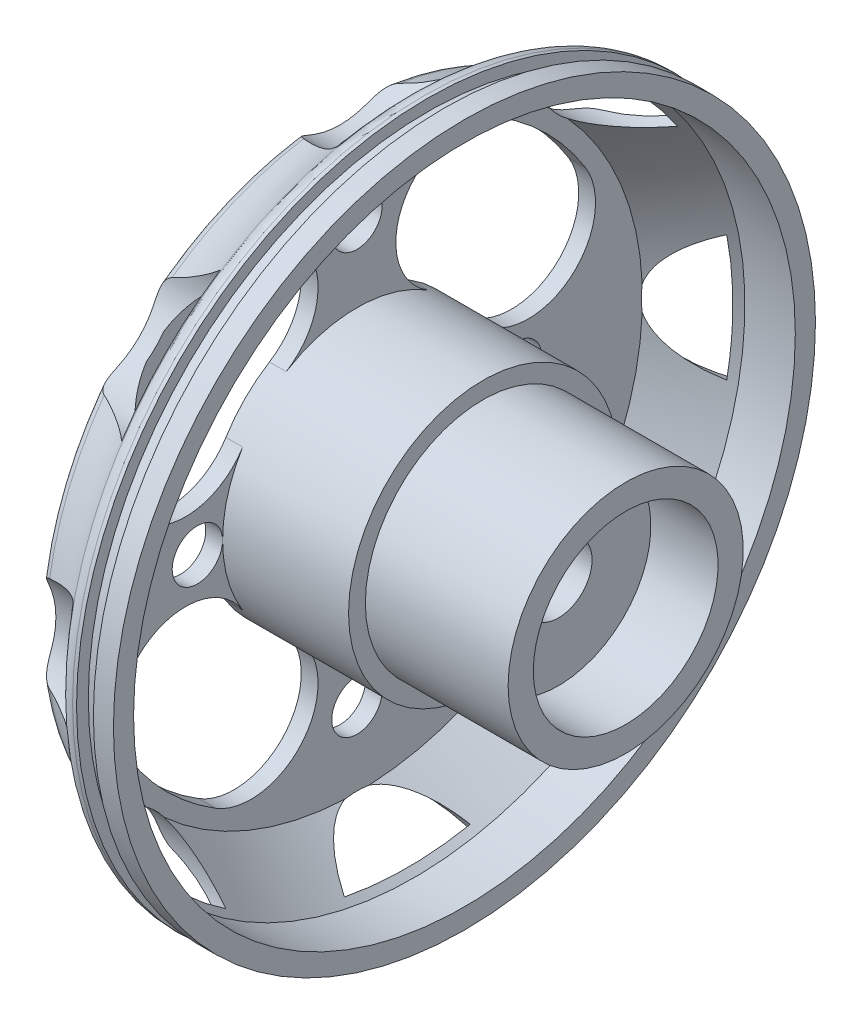
SolidWorks part; units mm, degrees
ref_plane "Front Plane" through (0, 0, 0) normal (0, 0, 1) x (1, 0, 0)
ref_plane "Top Plane" through (0, 0, 0) normal (0, 1, 0) x (1, 0, 0)
ref_plane "Right Plane" through (0, 0, 0) normal (1, 0, 0) x (0, 0, -1)
sketch "Sketch1" plane through (0, 0, 0) normal (0, 0, 1) x (1, 0, 0)
  line L0 (0, 143.0774) -> (0, 0) construction
  line L1 (0, 0) -> (157.1506, 0) construction
  line L2 (170, 55) -> (130, 55)
  line L3 (130, 55) -> (130, 20)
  line L4 (130, 20) -> (40, 20)
  line L5 (40, 20) -> (40, 55)
  line L6 (40, 55) -> (0, 55)
  line L7 (0, 55) -> (0, 87.7801)
  line L10 (74, 197) -> (44, 197)
  line L11 (44, 197) -> (10, 170)
  line L12 (10, 170) -> (10, 80)
  line L13 (10, 80) -> (85, 80)
  line L14 (85, 80) -> (85, 70)
  line L15 (85, 70) -> (170, 70)
  line L16 (170, 70) -> (170, 55)
  line L17 (74, 197) -> (74, 209)
  line L19 (0, 87.7801) -> (0, 180)
  line L20 (52.0391, 209) -> (45, 209)
  line L21 (52.0391, 209) -> (52.0391, 201.9891)
  line L22 (52.0391, 201.9891) -> (62.0706, 201.9891)
  line L23 (62.0706, 201.9891) -> (62.0706, 209)
  line L24 (62.0706, 209) -> (74, 209)
  arc A3 (0, 180) -> (45, 209) centre (-19.7325, 260.0332) ccw
  dimension "D12" = 45
  dimension "D1" = 20
  dimension "D2" = 40
  dimension "D3" = 55
  dimension "D4" = 10
  dimension "D5" = 70
  dimension "D6" = 80
  dimension "D7" = 40
  dimension "D8" = 45
  dimension "D9" = 170
  dimension "D10" = 55
  dimension "D11" = 90
  dimension "D13" = 12
  dimension "D14" = 30
  dimension "D15" = 29
  dimension "D16" = 209
  dimension "D17" = 180
  dimension "D18" = 15
revolve "Revolve1" add sketch "Sketch1" angle 360 about L1
fillet "Fillet1" radius 10 1 edges at (0, 0, 180)
fillet "Fillet2" radius 10 1 edges at (45, 0, 209)
sketch "Sketch5" plane through (0, 0, 0) normal (-1, 0, 0) x (0, 0, 1)
  line L0 (0, 205.6032) -> (0, 0) construction
  line L1 (0, 0) -> (205.6032, 0) construction
  line L2 (0, 0) -> (145.3834, 145.3834) construction
  circle A0 centre (0, 0) radius 205.6032 construction
  arc A1 (102.0401, 63.1492) -> (63.1492, 102.0401) centre (0, 0) ccw construction
  arc A2 (136.0534, 84.1989) -> (84.1989, 136.0534) centre (0, 0) ccw
  arc A3 (68.0267, 42.0995) -> (42.0995, 68.0267) centre (0, 0) ccw
  arc A4 (68.0267, 42.0995) -> (136.0534, 84.1989) centre (102.0401, 63.1492) ccw
  arc A5 (84.1989, 136.0534) -> (42.0995, 68.0267) centre (63.1492, 102.0401) ccw
  arc A6 (42.0995, -68.0267) -> (68.0267, -42.0995) centre (0, 0) ccw
  arc A7 (42.0995, -68.0267) -> (84.1989, -136.0534) centre (63.1492, -102.0401) ccw
  arc A8 (136.0534, -84.1989) -> (68.0267, -42.0995) centre (102.0401, -63.1492) ccw
  arc A9 (84.1989, -136.0534) -> (136.0534, -84.1989) centre (0, 0) ccw
  arc A10 (63.1492, -102.0401) -> (102.0401, -63.1492) centre (0, 0) ccw construction
  arc A11 (-68.0267, -42.0995) -> (-42.0995, -68.0267) centre (0, 0) ccw
  arc A12 (-68.0267, -42.0995) -> (-136.0534, -84.1989) centre (-102.0401, -63.1492) ccw
  arc A13 (-84.1989, -136.0534) -> (-42.0995, -68.0267) centre (-63.1492, -102.0401) ccw
  arc A14 (-136.0534, -84.1989) -> (-84.1989, -136.0534) centre (0, 0) ccw
  arc A15 (-102.0401, -63.1492) -> (-63.1492, -102.0401) centre (0, 0) ccw construction
  arc A16 (-42.0995, 68.0267) -> (-68.0267, 42.0995) centre (0, 0) ccw
  arc A17 (-42.0995, 68.0267) -> (-84.1989, 136.0534) centre (-63.1492, 102.0401) ccw
  arc A18 (-136.0534, 84.1989) -> (-68.0267, 42.0995) centre (-102.0401, 63.1492) ccw
  arc A19 (-84.1989, 136.0534) -> (-136.0534, 84.1989) centre (0, 0) ccw
  arc A20 (-63.1492, 102.0401) -> (-102.0401, 63.1492) centre (0, 0) ccw construction
  arc A21 (114.0961, 175.1087) -> (175.1087, 114.0961) centre (150.7971, 150.7971) ccw
  circle A22 centre (0, 0) radius 209 construction
  arc A23 (114.0961, 175.1087) -> (175.1087, 114.0961) centre (0, 0) cw
  arc A24 (204.4987, 43.1424) -> (204.4987, -43.1424) centre (0, 0) cw
  arc A25 (204.4987, 43.1424) -> (204.4987, -43.1424) centre (213.2593, 0) ccw
  arc A26 (175.1087, -114.0961) -> (114.0961, -175.1087) centre (0, 0) cw
  arc A27 (175.1087, -114.0961) -> (114.0961, -175.1087) centre (150.7971, -150.7971) ccw
  arc A28 (43.1424, -204.4987) -> (-43.1424, -204.4987) centre (0, 0) cw
  arc A29 (43.1424, -204.4987) -> (-43.1424, -204.4987) centre (0, -213.2593) ccw
  arc A30 (-114.0961, -175.1087) -> (-175.1087, -114.0961) centre (0, 0) cw
  arc A31 (-114.0961, -175.1087) -> (-175.1087, -114.0961) centre (-150.7971, -150.7971) ccw
  arc A32 (-204.4987, -43.1424) -> (-204.4987, 43.1424) centre (0, 0) cw
  arc A33 (-204.4987, -43.1424) -> (-204.4987, 43.1424) centre (-213.2593, 0) ccw
  arc A34 (-175.1087, 114.0961) -> (-114.0961, 175.1087) centre (0, 0) cw
  arc A35 (-175.1087, 114.0961) -> (-114.0961, 175.1087) centre (-150.7971, 150.7971) ccw
  arc A36 (-43.1424, 204.4987) -> (43.1424, 204.4987) centre (0, 0) cw
  arc A37 (-43.1424, 204.4987) -> (43.1424, 204.4987) centre (0, 213.2593) ccw
  point P10 (84.8528, 84.8528)
  point P20 (84.8528, -84.8528)
  point P27 (-84.8528, -84.8528)
  point P34 (-84.8528, 84.8528)
  point P39 (0, 0)
  point P67 (0, 0)
  dimension "D4" = 80
  dimension "D5" = 160
  dimension "D1" = 45
  dimension "D2" = 55
  dimension "D3" = 0
  dimension "D6" = 4
  dimension "D7" = 8
extrude "Cut-Extrude2" cut sketch "Sketch5" against normal blind 40
sketch "Sketch7" plane through (0, 0, 0) normal (-1, 0, 0) x (0, 0, 1)
  circle A0 centre (0, 0) radius 125 construction
  circle A1 centre (0, 0) radius 95 construction
  circle A2 centre (0, 125) radius 15
  circle A3 centre (0, -125) radius 15
  circle A4 centre (95, 0) radius 15
  circle A5 centre (-95, 0) radius 15
  dimension "D1" = 250
  dimension "D2" = 190
  dimension "D3" = 30
extrude "Cut-Extrude3" cut sketch "Sketch7" against normal blind 40
